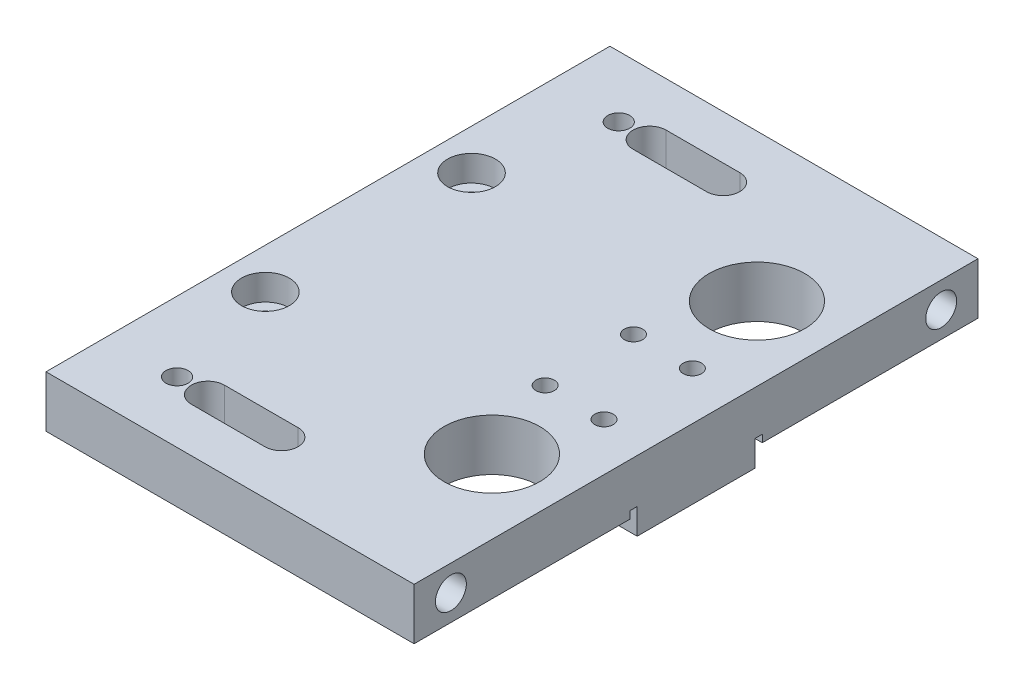
SolidWorks part; units mm, degrees
ref_plane "Front Plane" through (0, 0, 0) normal (0, 0, 1) x (1, 0, 0)
ref_plane "Top Plane" through (0, 0, 0) normal (0, 1, 0) x (1, 0, 0)
ref_plane "Right Plane" through (0, 0, 0) normal (1, 0, 0) x (0, 0, -1)
sketch "Sketch1" plane through (0, 0, 0) normal (0, 1, 0) x (1, 0, 0)
  line L1 (-15.2561, 19.8353) -> (34.7439, 19.8353)
  line L2 (-15.2561, 19.8353) -> (-15.2561, -56.7647)
  line L3 (-15.2561, -56.7647) -> (34.7439, -56.7647)
  line L4 (34.7439, 19.8353) -> (34.7439, -56.7647)
  line L5 (-1.5689, 13.7853) -> (8.4311, 13.7853)
  line L7 (-1.5689, 9.2853) -> (8.4311, 9.2853)
  line L9 (-1.5689, -46.2147) -> (8.4311, -46.2147)
  line L11 (-1.5689, -50.7147) -> (8.4311, -50.7147)
  circle A0 centre (24.714, -0.1647) radius 6.5
  circle A1 centre (24.714, -36.1647) radius 6.5
  circle A2 centre (-9.7561, -4.4647) radius 1.75
  circle A3 centre (-9.7561, -32.4647) radius 1.75
  arc A4 (-1.5689, -46.2147) -> (-1.5689, -50.7147) centre (-1.5689, -48.4647) ccw
  arc A5 (8.4311, -50.7147) -> (8.4311, -46.2147) centre (8.4311, -48.4647) ccw
  arc A6 (8.4311, 9.2853) -> (8.4311, 13.7853) centre (8.4311, 11.5353) ccw
  arc A7 (-1.5689, 13.7853) -> (-1.5689, 9.2853) centre (-1.5689, 11.5353) ccw
  circle A8 centre (-5.7561, -48.4647) radius 1.5
  circle A9 centre (-5.7561, 11.5353) radius 1.5
  dimension "D4" = 5.5
  dimension "D5" = 3.5
  dimension "D6" = 24.3
  dimension "D7" = 36
  dimension "D8" = 13
  dimension "D9" = 20
  dimension "D12" = 3
  dimension "D13" = 3
  dimension "D16" = 9.5
  dimension "D1" = 50
  dimension "D2" = 76.6
  dimension "D3" = 28
  dimension "D10" = 10
  dimension "D11" = 10
  dimension "D14" = 4.5
  dimension "D15" = 4.1872
extrude "Boss-Extrude1" add sketch "Sketch1" along normal blind 7
hole_wizard "M5 Tapped Hole1" positions "Sketch2" profile "Sketch3" tap size "M5" standard "ISO"
sketch "Sketch2" plane through (34.7439, 0, 0) normal (1, 0, 0) x (0, 0, -1)
  line L0 (-56.7647, 0) -> (19.8353, 0) construction
  line L1 (-56.7647, 7) -> (-56.7647, 0) construction
  point P0 (14.8358, 3.5)
  point P2 (-51.7647, 3.5)
  dimension "D1" = 3.5
  dimension "D2" = 5
  dimension "D3" = 3.5
sketch "Sketch3" plane through (34.7439, 3.5, -14.8358) normal (0, 1, 0) x (0, 0, -1)
  line L0 (0, 0) -> (0, 11.2618)
  line L1 (0, 11.2618) -> (2.1, 10)
  line L2 (2.1, 10) -> (2.1, 0)
  line L5 (2.1, 0) -> (0, 0)
  line L10 (0, 11.2618) -> (-2.1, 10) construction
  line L11 (0, -6.35) -> (0, 107.95) construction
  dimension "Tap Drill Dia." = 4.2
  dimension "Tap Drill Depth" = 10
  dimension "Drill Angle" = 118
cosmetic thread "Hole Thread1" parameters "D1"=10, "D2"=5
cosmetic thread "Hole Thread2" parameters "D1"=10, "D2"=5
sketch "Sketch4" plane through (0, 7, 0) normal (0, 1, 0) x (1, 0, 0)
  circle A0 centre (-9.7561, -4.4647) radius 3.25
  circle A1 centre (-9.7561, -32.4647) radius 3.25
  dimension "D1" = 6.5
  dimension "D2" = 6.5
extrude "Cut-Extrude1" cut sketch "Sketch4" against normal blind 3.5
hole_wizard "M3 Tapped Hole1" positions "Sketch5" profile "Sketch6" tap size "M3" standard "ISO"
sketch "Sketch5" plane through (0, 7, 0) normal (0, 1, 0) x (1, 0, 0)
  line L0 (-15.2561, 19.8353) -> (-15.2561, -56.7647) construction
  line L2 (34.7439, 19.8353) -> (-15.2561, 19.8353) construction
  point P0 (20.2439, -12.4647)
  point P2 (28.2439, -12.4647)
  point P4 (28.2439, -24.4647)
  point P6 (20.2439, -24.4647)
  dimension "D1" = 12
  dimension "D2" = 35.5
  dimension "D3" = 32.3
  dimension "D4" = 43.5
  dimension "D5" = 43.5
cosmetic thread "Hole Thread3" parameters "D1"=6, "D2"=3
cosmetic thread "Hole Thread4" parameters "D1"=6, "D2"=3
cosmetic thread "Hole Thread5" parameters "D1"=6, "D2"=3
cosmetic thread "Hole Thread6" parameters "D1"=6, "D2"=3
sketch "Sketch6" plane through (20.2439, 7, 12.4647) normal (1, 0, 0) x (0, 0, 1)
  line L0 (0, 0) -> (0, 20.7511)
  line L1 (0, 20.7511) -> (1.25, 20)
  line L2 (1.25, 20) -> (1.25, 0)
  line L5 (1.25, 0) -> (0, 0)
  line L10 (0, 20.7511) -> (-1.25, 20) construction
  line L11 (0, -6.35) -> (0, 107.95) construction
  dimension "Tap Drill Dia." = 2.5
  dimension "Tap Drill Depth" = 20
  dimension "Drill Angle" = 118
cosmetic thread "Hole Thread8" parameters "D1"=6, "D2"=3
cosmetic thread "Hole Thread9" parameters "D1"=6, "D2"=3
sketch3d "3DSketch1"
  point P0 (11.4536, 0, 24.9935)
sketch "Sketch10" plane through (0, 0, 0) normal (0, -1, 0) x (1, 0, 0)
  line L0 (34.7439, 56.7647) -> (34.7439, -19.8353) construction
  line L1 (34.7439, 27.4647) -> (-15.2561, 27.4647)
  line L2 (34.7439, 27.4647) -> (34.7439, 9.4647)
  line L3 (34.7439, 9.4647) -> (-15.2561, 9.4647)
  line L4 (-15.2561, 27.4647) -> (-15.2561, 9.4647)
  line L5 (-15.2561, -19.8353) -> (-15.2561, 56.7647) construction
  line L6 (34.7439, -19.8353) -> (-15.2561, -19.8353) construction
  dimension "D1" = 18
  dimension "D2" = 29.3
extrude "Cut-Extrude3" cut sketch "Sketch10" against normal blind 1
sketch "Sketch11" plane through (0, 1, 0) normal (0, -1, 0) x (1, 0, 0)
  line L0 (34.7439, 9.4647) -> (34.7439, 27.4647) construction
  line L1 (34.7439, 26.4647) -> (-15.2561, 26.4647)
  line L2 (34.7439, 26.4647) -> (34.7439, 10.4647)
  line L3 (34.7439, 10.4647) -> (-15.2561, 10.4647)
  line L4 (-15.2561, 26.4647) -> (-15.2561, 10.4647)
  line L5 (-15.2561, 27.4647) -> (-15.2561, 9.4647) construction
  line L6 (-15.2561, 9.4647) -> (34.7439, 9.4647) construction
  line L7 (34.7439, 27.4647) -> (-15.2561, 27.4647) construction
  dimension "D1" = 1
  dimension "D2" = 1
extrude "Boss-Extrude2" add sketch "Sketch11" along normal blind 3.5
hole_wizard "M3 Tapped Hole2" positions "Sketch12" profile "Sketch13" tap size "M3" standard "ISO"
sketch "Sketch12" plane through (0, -2.5, 0) normal (0, -1, 0) x (-1, 0, 0)
  point P0 (-20.2439, -12.4647)
  point P3 (-28.2439, -12.4647)
  point P6 (-20.2439, -24.4647)
  point P9 (-28.2439, -24.4647)
  point P12 (-47.0683, 0)
sketch "Sketch13" plane through (20.2439, -2.5, 12.4647) normal (1, 0, 0) x (0, 0, -1)
  line L0 (0, 0) -> (0, 20.7511)
  line L1 (0, 20.7511) -> (1.25, 20)
  line L2 (1.25, 20) -> (1.25, 0)
  line L5 (1.25, 0) -> (0, 0)
  line L10 (0, 20.7511) -> (-1.25, 20) construction
  line L11 (0, -6.35) -> (0, 107.95) construction
  dimension "Tap Drill Dia." = 2.5
  dimension "Tap Drill Depth" = 20
  dimension "Drill Angle" = 118
cosmetic thread "Hole Thread7" parameters "D1"=6, "D2"=3
cosmetic thread "Hole Thread10" parameters "D1"=6, "D2"=3
